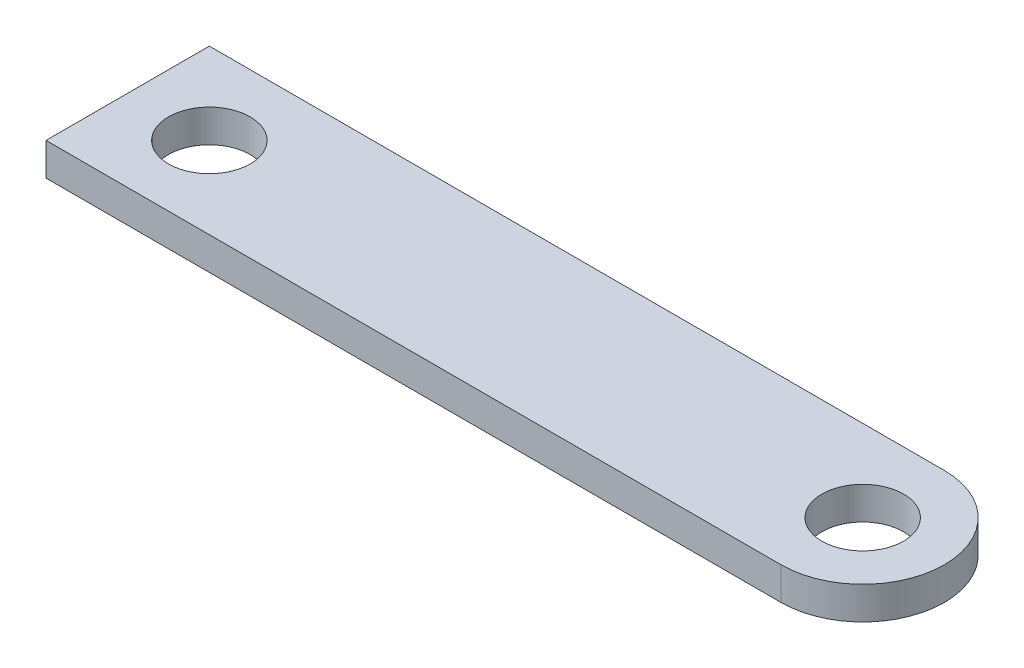
SolidWorks part; units mm, degrees
ref_plane "Alzado" through (0, 0, 0) normal (0, 0, 1) x (1, 0, 0)
ref_plane "Planta" through (0, 0, 0) normal (0, 1, 0) x (1, 0, 0)
ref_plane "Vista lateral" through (0, 0, 0) normal (1, 0, 0) x (0, 0, -1)
sketch "Croquis1" plane through (0, 0, 0) normal (0, 1, 0) x (1, 0, 0)
  line L1 (-22.5, -5) -> (22.5, -5)
  line L2 (-22.5, -5) -> (-22.5, 5)
  line L3 (-22.5, 5) -> (22.5, 5)
  line L4 (22.5, -5) -> (22.5, 5)
  line L5 (-22.5, -5) -> (22.5, 5) construction
  line L6 (-22.5, 5) -> (22.5, -5) construction
  circle A0 centre (22.5, 0) radius 5
  circle A1 centre (22.5, 0) radius 2.5
  circle A2 centre (-17.5, 0) radius 2.5
  point P0 (0, 0)
  dimension "D3" = 5
  dimension "D4" = 5
  dimension "D1" = 45
  dimension "D2" = 10
  dimension "D5" = 5
extrude "Saliente-Extruir2" add sketch "Croquis1" along normal blind 2 contours A0 L3 L2 L1 | A1 L4 A0 | A1 L4 A0
